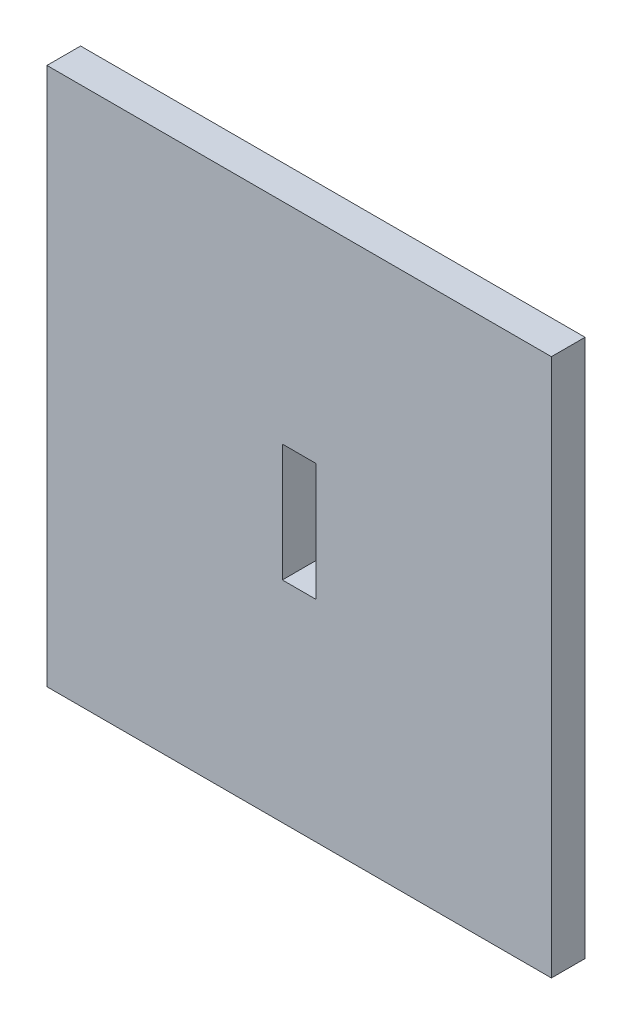
SolidWorks part; units mm, degrees
material "Malleable Cast Iron"
ref_plane "Front Plane" through (0, 0, 0) normal (0, 0, 1) x (1, 0, 0)
ref_plane "Top Plane" through (0, 0, 0) normal (0, 1, 0) x (1, 0, 0)
ref_plane "Right Plane" through (0, 0, 0) normal (1, 0, 0) x (0, 0, -1)
sketch "Sketch1" plane through (0, 0, 0) normal (0, 0, 1) x (1, 0, 0)
  line L1 (-15, -16) -> (15, -16)
  line L2 (-15, -16) -> (-15, 16)
  line L3 (-15, 16) -> (15, 16)
  line L4 (15, -16) -> (15, 16)
  line L5 (-15, -16) -> (15, 16) construction
  line L6 (-15, 16) -> (15, -16) construction
  line L7 (1, -3.5) -> (-1, -3.5)
  line L8 (1, -3.5) -> (1, 3.5)
  line L9 (1, 3.5) -> (-1, 3.5)
  line L10 (-1, -3.5) -> (-1, 3.5)
  line L11 (1, -3.5) -> (-1, 3.5) construction
  line L12 (1, 3.5) -> (-1, -3.5) construction
  point P0 (0, 0)
  point P6 (0, 0)
  dimension "D1" = 32
  dimension "D2" = 7
  dimension "D3" = 2
  dimension "D4" = 30
extrude "Boss-Extrude1" add sketch "Sketch1" along normal blind 2
